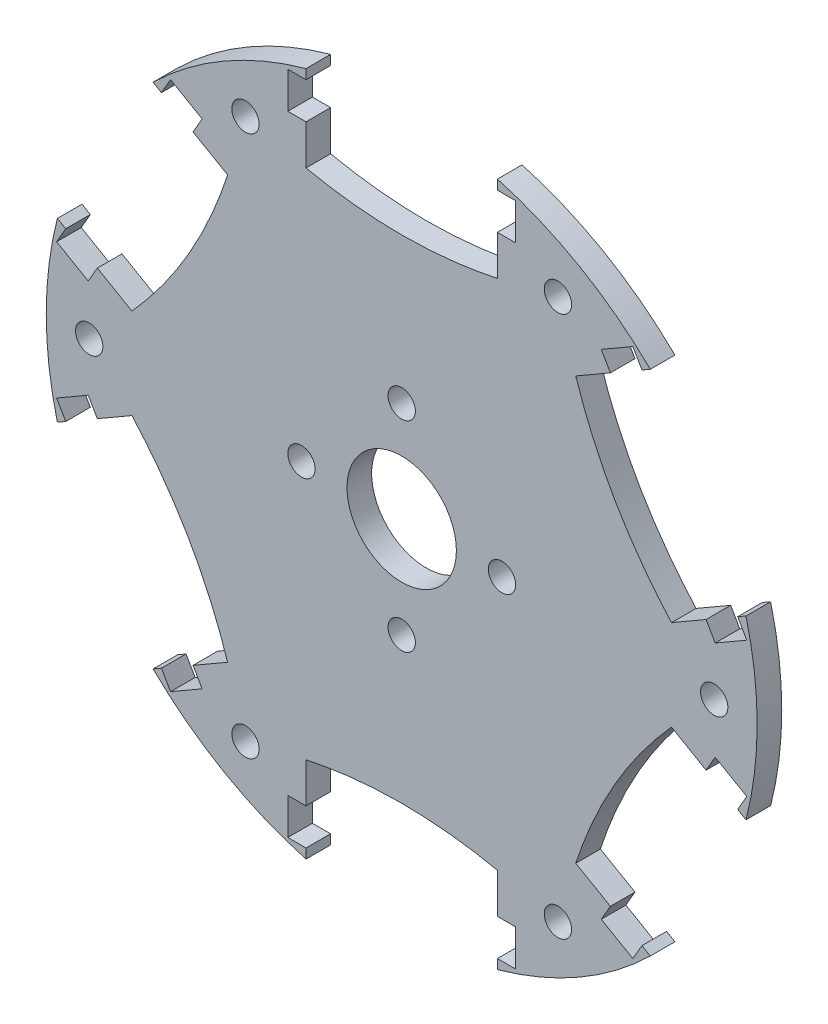
SolidWorks part; units mm, degrees
ref_plane "Alzado" through (0, 0, 0) normal (0, 0, 1) x (1, 0, 0)
ref_plane "Planta" through (0, 0, 0) normal (0, 1, 0) x (1, 0, 0)
ref_plane "Vista lateral" through (0, 0, 0) normal (1, 0, 0) x (0, 0, -1)
sketch "Croquis2" plane through (0, 0, 0) normal (0, 0, 1) x (1, 0, 0)
  line L0 (0, 0) -> (0, 41) construction
  line L1 (-9.5, 34.5) -> (9.5, 34.5) construction
  line L2 (0, 0) -> (41, 0) construction
  line L3 (-9.5, 29.1158) -> (-9.5, 39.8842) construction
  line L4 (9.5, 29.1158) -> (9.5, 39.8842) construction
  line L5 (-10.5, 37.56) -> (-10.5, 28.1158)
  line L6 (10.5, 37.56) -> (10.5, 28.1158)
  line L7 (27.2779, 27.8732) -> (19.099, 23.1512)
  line L8 (37.7779, 9.6867) -> (29.599, 4.9646)
  line L9 (37.7779, -9.6867) -> (29.599, -4.9646)
  line L10 (27.2779, -27.8732) -> (19.099, -23.1512)
  line L11 (10.5, -37.56) -> (10.5, -28.1158)
  line L12 (-10.5, -37.56) -> (-10.5, -28.1158)
  line L13 (-27.2779, -27.8732) -> (-19.099, -23.1512)
  line L14 (-37.7779, -9.6867) -> (-29.599, -4.9646)
  line L15 (-37.7779, 9.6867) -> (-29.599, 4.9646)
  line L16 (-27.2779, 27.8732) -> (-19.099, 23.1512)
  line L17 (10.5, 28.1158) -> (19.099, 23.1512) construction
  line L18 (0, 0) -> (17.892, 30.9899) construction
  circle A0 centre (0, 0) radius 41 construction
  circle A1 centre (0, 0) radius 39
  circle A2 centre (0, 0) radius 6
  circle A3 centre (0, 0) radius 35.7841 construction
  circle A5 centre (17.142, 29.6909) radius 1.5
  circle A6 centre (34.2841, 0) radius 1.5
  circle A7 centre (17.142, -29.6909) radius 1.5
  circle A8 centre (-17.142, -29.6909) radius 1.5
  circle A9 centre (-34.2841, 0) radius 1.5
  circle A10 centre (-17.142, 29.6909) radius 1.5
  spline S0 degree 2 poles (-9.5, 29.1158) (0, 26.8842) (9.5, 29.1158) knots 0 0 0 1 1 1 construction
  spline S1 degree 2 poles (-10.5, 28.1158) (0, 25.8842) (10.5, 28.1158) knots 0 0 0 1 1 1
  spline S2 degree 2 poles (19.099, 23.1512) (22.4164, 12.9421) (29.599, 4.9646) knots 0 0 0 1 1 1
  spline S3 degree 2 poles (29.599, -4.9646) (22.4164, -12.9421) (19.099, -23.1512) knots 0 0 0 1 1 1
  spline S4 degree 2 poles (10.5, -28.1158) (0, -25.8842) (-10.5, -28.1158) knots 0 0 0 1 1 1
  spline S5 degree 2 poles (-19.099, -23.1512) (-22.4164, -12.9421) (-29.599, -4.9646) knots 0 0 0 1 1 1
  spline S6 degree 2 poles (-29.599, 4.9646) (-22.4164, 12.9421) (-19.099, 23.1512) knots 0 0 0 1 1 1
  point P6 (0, 34.5)
  point P46 (14.7995, 25.6335)
  dimension "D1" = 82
  dimension "D4" = 78
  dimension "D10" = 12
  dimension "D11" = 3
  dimension "D12" = 6
  dimension "D2" = 34.5
  dimension "D3" = 19
  dimension "D5" = 6.5
  dimension "D6" = 1
  dimension "D7" = 1
  dimension "D8" = 1
  dimension "D9" = 6
extrude "Saliente-Extruir2" add sketch "Croquis2" along normal blind 2.7 contours S6 L15 A1 L14 S5 L13 L12 S4 L11 L10 S3 L9 L8 S2 L7 L6 S1 L5 L16 A10 A9 A8 A7 A6 A5 A2
sketch "Croquis3" plane through (0, 0, 2.7) normal (0, 0, 1) x (1, 0, 0)
  line L0 (0, 0) -> (0, 41) construction
  line L1 (-12.5, 34.5) -> (12.5, 34.5) construction
  line L2 (0, 0) -> (41, 0) construction
  line L3 (-10.5, 36.5) -> (-12.5, 36.5)
  line L4 (-10.5, 37.56) -> (-10.5, 28.1158) construction
  line L5 (-12.5, 36.5) -> (-12.5, 32.5)
  line L6 (-10.5, 32.5) -> (-12.5, 32.5)
  line L7 (-10.5, 36.5) -> (-10.5, 32.5)
  line L8 (10.5, 36.5) -> (12.5, 36.5)
  line L9 (12.5, 36.5) -> (12.5, 32.5)
  line L10 (10.5, 32.5) -> (12.5, 32.5)
  line L11 (10.5, 36.5) -> (10.5, 32.5)
  line L12 (22.8958, 25.3433) -> (21.8958, 27.0753)
  line L13 (26.3599, 27.3433) -> (22.8958, 25.3433)
  line L14 (25.3599, 29.0753) -> (21.8958, 27.0753)
  line L15 (26.3599, 27.3433) -> (25.3599, 29.0753)
  line L16 (36.8599, 9.1567) -> (37.8599, 7.4247)
  line L17 (37.8599, 7.4247) -> (34.3958, 5.4247)
  line L18 (33.3958, 7.1567) -> (34.3958, 5.4247)
  line L19 (36.8599, 9.1567) -> (33.3958, 7.1567)
  line L20 (33.3958, -7.1567) -> (34.3958, -5.4247)
  line L21 (36.8599, -9.1567) -> (33.3958, -7.1567)
  line L22 (37.8599, -7.4247) -> (34.3958, -5.4247)
  line L23 (36.8599, -9.1567) -> (37.8599, -7.4247)
  line L24 (26.3599, -27.3433) -> (25.3599, -29.0753)
  line L25 (25.3599, -29.0753) -> (21.8958, -27.0753)
  line L26 (22.8958, -25.3433) -> (21.8958, -27.0753)
  line L27 (26.3599, -27.3433) -> (22.8958, -25.3433)
  line L28 (10.5, -32.5) -> (12.5, -32.5)
  line L29 (10.5, -36.5) -> (10.5, -32.5)
  line L30 (12.5, -36.5) -> (12.5, -32.5)
  line L31 (10.5, -36.5) -> (12.5, -36.5)
  line L32 (-10.5, -36.5) -> (-12.5, -36.5)
  line L33 (-12.5, -36.5) -> (-12.5, -32.5)
  line L34 (-10.5, -32.5) -> (-12.5, -32.5)
  line L35 (-10.5, -36.5) -> (-10.5, -32.5)
  line L36 (-22.8958, -25.3433) -> (-21.8958, -27.0753)
  line L37 (-26.3599, -27.3433) -> (-22.8958, -25.3433)
  line L38 (-25.3599, -29.0753) -> (-21.8958, -27.0753)
  line L39 (-26.3599, -27.3433) -> (-25.3599, -29.0753)
  line L40 (-36.8599, -9.1567) -> (-37.8599, -7.4247)
  line L41 (-37.8599, -7.4247) -> (-34.3958, -5.4247)
  line L42 (-33.3958, -7.1567) -> (-34.3958, -5.4247)
  line L43 (-36.8599, -9.1567) -> (-33.3958, -7.1567)
  line L44 (-33.3958, 7.1567) -> (-34.3958, 5.4247)
  line L45 (-36.8599, 9.1567) -> (-33.3958, 7.1567)
  line L46 (-37.8599, 7.4247) -> (-34.3958, 5.4247)
  line L47 (-36.8599, 9.1567) -> (-37.8599, 7.4247)
  line L48 (-26.3599, 27.3433) -> (-25.3599, 29.0753)
  line L49 (-25.3599, 29.0753) -> (-21.8958, 27.0753)
  line L50 (-22.8958, 25.3433) -> (-21.8958, 27.0753)
  line L51 (-26.3599, 27.3433) -> (-22.8958, 25.3433)
  line L52 (35.1279, -8.1567) -> (24.6279, -26.3433) construction
  line L53 (0, 0) -> (29.8779, -17.25) construction
  circle A0 centre (0, 0) radius 11 construction
  circle A1 centre (11, 0) radius 1.5
  circle A2 centre (0, -11) radius 1.5
  circle A3 centre (-11, 0) radius 1.5
  circle A4 centre (0, 11) radius 1.5
  circle A5 centre (0, 0) radius 41 construction
  point P15 (0, 34.5)
  dimension "D1" = 22
  dimension "D2" = 3
  dimension "D4" = 82
  dimension "D5" = 34.5
  dimension "D6" = 25
  dimension "D7" = 2
  dimension "D8" = 6
  dimension "D3" = 4
extrude "Cortar-Extruir1" cut sketch "Croquis3" against normal through all and the other way through all
